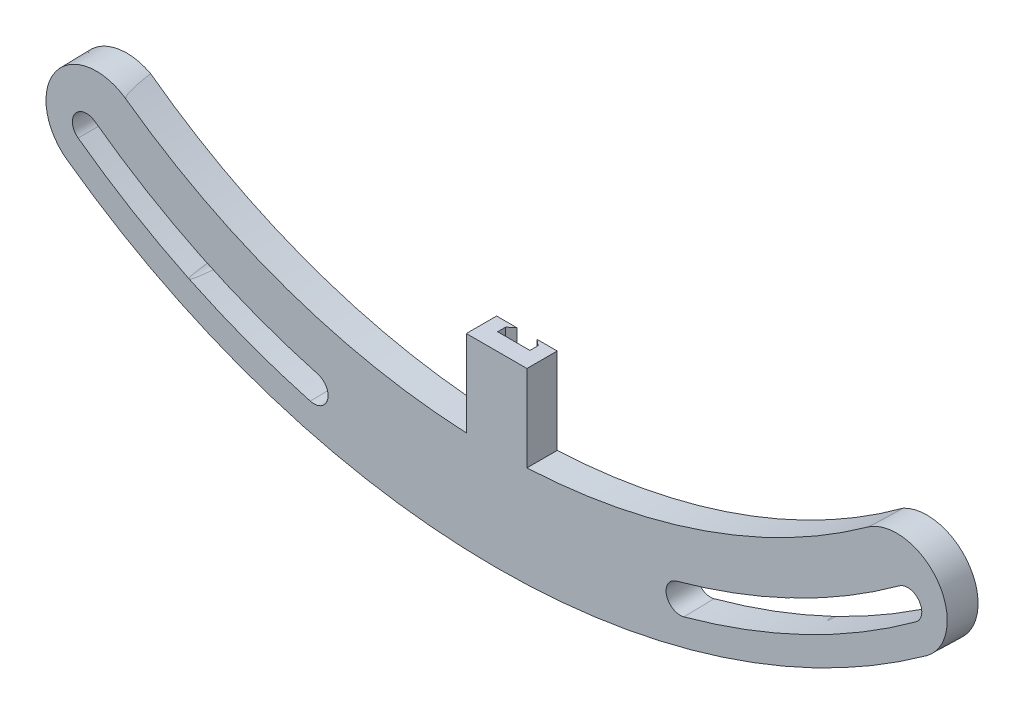
SolidWorks part; units mm, degrees
ref_plane "Front Plane" through (0, 0, 0) normal (0, 0, 1) x (1, 0, 0)
ref_plane "Top Plane" through (0, 0, 0) normal (0, 1, 0) x (1, 0, 0)
ref_plane "Right Plane" through (0, 0, 0) normal (1, 0, 0) x (0, 0, -1)
sketch "Sketch1" plane through (0, 0, 0) normal (1, 0, 0) x (0, 0, -1)
  line L0 (0, 92.456) -> (-3.81, 92.456)
  line L1 (-3.81, 92.456) -> (-3.81, 79.756)
  line L2 (-3.81, 79.756) -> (0, 79.756)
  line L4 (0, 79.756) -> (0, 92.456)
  line L6 (0, 0) -> (62.4328, 0) construction
  dimension "D1" = 79.756
  dimension "D2" = 3.81
  dimension "D3" = 12.7
revolve "Revolve1" add sketch "Sketch1" angle 360 about L6
sketch "Sketch2" plane through (0, 0, 3.81) normal (0, 0, 1) x (1, 0, 0)
  circle A0 centre (0, 87.376) radius 1.778
  circle A1 centre (68.3133, 54.478) radius 1.778
  circle A2 centre (0, 0) radius 92.456 construction
  circle A3 centre (85.1853, -19.443) radius 1.778
  circle A4 centre (37.911, -78.7231) radius 1.778
  circle A5 centre (-37.911, -78.7231) radius 1.778
  circle A6 centre (-85.1853, -19.443) radius 1.778
  circle A7 centre (-68.3133, 54.478) radius 1.778
  dimension "D1" = 3.556
  dimension "D2" = 87.376
  dimension "D3" = 7
extrude "Cut-Extrude1" cut sketch "Sketch2" against normal through all
sketch "Sketch3" plane through (0, 0, 3.81) normal (0, 0, 1) x (1, 0, 0)
  line L0 (0, 0) -> (0, -118.5535) construction
  line L1 (0, 0) -> (-55.1972, -65.7814) construction
  line L2 (0, 0) -> (55.1972, -65.7814) construction
  arc A0 (-46.6209, -64.711) -> (46.6209, -64.711) centre (0, 0) ccw
  arc A1 (-54.0446, -75.0153) -> (54.0446, -75.0153) centre (0, 0) ccw
  arc A2 (-46.6209, -64.711) -> (-54.0446, -75.0153) centre (-50.3328, -69.8631) ccw
  arc A3 (54.0446, -75.0153) -> (46.6209, -64.711) centre (50.3328, -69.8631) ccw
  arc A4 (-51.5829, -70.5249) -> (-22.9772, -84.3007) centre (0, 0) ccw construction
  arc A5 (-52.6326, -71.96) -> (-23.4447, -86.0162) centre (0, 0) ccw
  arc A6 (-50.5333, -69.0898) -> (-22.5096, -82.5853) centre (0, 0) ccw
  arc A7 (-50.5333, -69.0898) -> (-52.6326, -71.96) centre (-51.5829, -70.5249) ccw
  arc A8 (-23.4447, -86.0162) -> (-22.5096, -82.5853) centre (-22.9772, -84.3007) ccw
  circle A10 centre (-37.911, -78.7231) radius 1.778 construction
  arc A36 (23.096, -84.3007) -> (51.7017, -70.5249) centre (0.1188, 0) ccw construction
  arc A37 (23.5635, -86.0162) -> (52.7514, -71.96) centre (0.1188, 0) ccw
  arc A38 (22.6284, -82.5853) -> (50.6521, -69.0898) centre (0.1188, 0) ccw
  arc A39 (22.6284, -82.5853) -> (23.5635, -86.0162) centre (23.096, -84.3007) ccw
  arc A40 (52.7514, -71.96) -> (50.6521, -69.0898) centre (51.7017, -70.5249) ccw
  arc A222 (-87.3741, -3.5495) -> (-80.3091, -34.5035) centre (-0.0741, 0.0929) ccw construction
  arc A223 (-89.1506, -3.6237) -> (-81.9418, -35.2075) centre (-0.0741, 0.0929) ccw
  arc A224 (-85.5977, -3.4754) -> (-78.6764, -33.7995) centre (-0.0741, 0.0929) ccw
  arc A225 (-85.5977, -3.4754) -> (-89.1506, -3.6237) centre (-87.3741, -3.5495) ccw
  arc A226 (-81.9418, -35.2075) -> (-78.6764, -33.7995) centre (-80.3091, -34.5035) ccw
  arc A227 (-57.3261, 66.1916) -> (-77.1219, 41.3684) centre (-0.0476, 0.2087) ccw construction
  arc A228 (-58.4916, 67.5343) -> (-78.6902, 42.206) centre (-0.0476, 0.2087) ccw
  arc A229 (-56.1605, 64.8489) -> (-75.5535, 40.5309) centre (-0.0476, 0.2087) ccw
  arc A230 (-56.1605, 64.8489) -> (-58.4916, 67.5343) centre (-57.3261, 66.1916) ccw
  arc A231 (-78.6902, 42.206) -> (-75.5535, 40.5309) centre (-77.1219, 41.3684) ccw
  arc A232 (15.9344, 86.182) -> (-15.8156, 86.182) centre (0.0594, 0.2602) ccw construction
  arc A233 (16.2574, 87.9304) -> (-16.1386, 87.9304) centre (0.0594, 0.2602) ccw
  arc A234 (15.6114, 84.4336) -> (-15.4926, 84.4336) centre (0.0594, 0.2602) ccw
  arc A235 (15.6114, 84.4336) -> (16.2574, 87.9304) centre (15.9344, 86.182) ccw
  arc A236 (-16.1386, 87.9304) -> (-15.4926, 84.4336) centre (-15.8156, 86.182) ccw
  arc A237 (77.2407, 41.3684) -> (57.4449, 66.1916) centre (0.1664, 0.2087) ccw construction
  arc A238 (78.809, 42.206) -> (58.6104, 67.5343) centre (0.1664, 0.2087) ccw
  arc A239 (75.6723, 40.5309) -> (56.2793, 64.8489) centre (0.1664, 0.2087) ccw
  arc A240 (75.6723, 40.5309) -> (78.809, 42.206) centre (77.2407, 41.3684) ccw
  arc A241 (58.6104, 67.5343) -> (56.2793, 64.8489) centre (57.4449, 66.1916) ccw
  arc A242 (80.4279, -34.5035) -> (87.4929, -3.5495) centre (0.1928, 0.0929) ccw construction
  arc A243 (82.0605, -35.2075) -> (89.2693, -3.6237) centre (0.1928, 0.0929) ccw
  arc A244 (78.7952, -33.7995) -> (85.7164, -3.4754) centre (0.1928, 0.0929) ccw
  arc A245 (78.7952, -33.7995) -> (82.0605, -35.2075) centre (80.4279, -34.5035) ccw
  arc A246 (89.2693, -3.6237) -> (85.7164, -3.4754) centre (87.4929, -3.5495) ccw
  point P12 (-37.911, -78.7231)
  point P29 (-68.3133, 54.478)
  point P37 (0, 87.376)
  point P45 (68.3133, 54.478)
  point P53 (85.1853, -19.443)
  point P68 (38.0298, -78.7231)
  point P77 (-85.1853, -19.443)
  point P89 (-85.1853, -19.443)
  point P97 (-68.3133, 54.478)
  point P105 (0, 87.376)
  point P113 (68.3133, 54.478)
  point P121 (85.1853, -19.443)
  point P129 (-85.1853, -19.443)
  point P137 (-68.3133, 54.478)
  point P145 (0, 87.376)
  point P153 (68.3133, 54.478)
  point P161 (85.1853, -19.443)
  point P169 (-85.1853, -19.443)
  point P177 (-68.3133, 54.478)
  point P185 (0, 87.376)
  point P193 (68.3133, 54.478)
  point P201 (85.1853, -19.443)
  point P209 (-85.1853, -19.443)
  point P217 (-68.3133, 54.478)
  point P225 (0, 87.376)
  point P233 (68.3133, 54.478)
  point P241 (85.1853, -19.443)
  point P249 (-85.1853, -19.443)
  point P257 (-68.3133, 54.478)
  point P265 (0, 87.376)
  point P273 (68.3133, 54.478)
  point P281 (85.1853, -19.443)
  point P289 (-85.1853, -19.443)
  point P297 (-68.3133, 54.478)
  point P305 (0, 87.376)
  point P313 (68.3133, 54.478)
  point P321 (85.1853, -19.443)
  point P329 (-85.2594, -19.3501)
  point P337 (-68.3609, 54.6867)
  point P345 (0.0594, 87.6362)
  point P353 (68.4797, 54.6867)
  point P361 (85.3781, -19.3501)
  point P369 (-85.2594, -19.3501)
  point P377 (-68.3609, 54.6867)
  point P385 (0.0594, 87.6362)
  point P393 (68.4797, 54.6867)
  point P401 (85.3781, -19.3501)
  dimension "D3" = 79.756
  dimension "D4" = 92.456
  dimension "D5" = 31.75
  dimension "D1" = 40
  dimension "D2" = 40
  dimension "D6" = 7
extrude "Cut-Extrude15" cut sketch "Sketch3" against normal through all draft 1 flip side to cut
ref_plane "Plane1" through (0, -79.756, 0) normal (0, -1, 0) x (1, 0, 0)
sketch "Sketch8" plane through (0, -79.756, 0) normal (0, -1, 0) x (1, 0, 0)
  line L0 (46.6209, 3.81) -> (-46.6209, 3.81) construction
  line L1 (-3.81, 3.81) -> (3.81, 3.81)
  line L2 (-3.81, 3.81) -> (-3.81, 0)
  line L3 (-3.81, 0) -> (3.81, 0)
  line L4 (3.81, 3.81) -> (3.81, 0)
  line L5 (-47.3375, 0) -> (47.3375, 0) construction
  dimension "D1" = 3.81
  dimension "D2" = 7.62
extrude "Boss-Extrude1" add sketch "Sketch8" against normal blind 10.922
sketch "Sketch9" plane through (0, -68.834, 0) normal (0, 1, 0) x (1, 0, 0)
  line L1 (1.27, 0) -> (-1.27, 0)
  line L2 (2.032, -0.635) -> (2.032, -1.651)
  line L3 (2.032, -1.651) -> (-2.032, -1.651)
  line L4 (-2.032, -0.635) -> (-2.032, -1.651)
  line L5 (-1.27, 0) -> (-2.032, -0.635)
  line L6 (1.27, 0) -> (2.032, -0.635)
  dimension "D1" = 1.651
  dimension "D3" = 2.032
  dimension "D4" = 1.016
  dimension "D5" = 0.762
extrude "Cut-Extrude16" cut sketch "Sketch9" against normal blind 6.096
